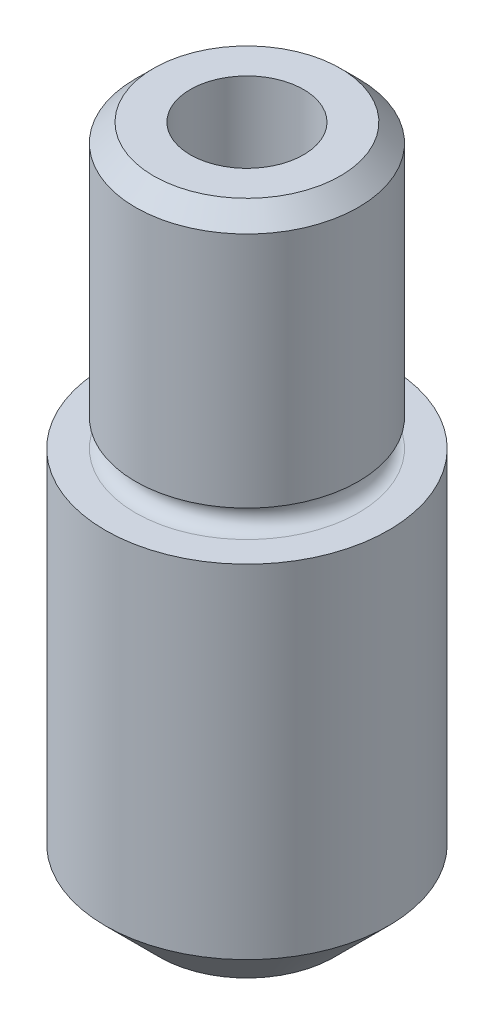
SolidWorks part; units mm, degrees
material "18-8 SS"
ref_plane "Front" through (0, 0, 0) normal (0, 0, 1) x (1, 0, 0)
ref_plane "Top" through (0, 0, 0) normal (0, 1, 0) x (1, 0, 0)
ref_plane "Right" through (0, 0, 0) normal (1, 0, 0) x (0, 0, -1)
sketch "Sketch1" plane through (0, 0, 0) normal (0, 1, 0) x (1, 0, 0)
  circle A0 centre (0, 0) radius 1.985
  dimension "D1" = 3.97
extrude "Base-Extrude" add sketch "Sketch1" along normal blind 9.525
sketch "Sketch2" plane through (0, 9.525, 0) normal (0, 1, 0) x (1, 0, 0)
  circle A0 centre (0, 0) radius 1.5621
  circle A1 centre (0, 0) radius 1.985
  circle A2 centre (0, 0) radius 1.985 construction
  dimension "D1" = 3.1242
extrude "Cut-Extrude2" cut sketch "Sketch2" against normal blind 3.9624
chamfer "Chamfer1" distance 0.254 angle 45 1 edges at (0, 9.525, 1.5621)
chamfer "Chamfer2" distance 0.762 angle 45 1 edges at (0, 0, 1.985)
sketch "Sketch4" plane through (0, 0, 0) normal (0, 0, 1) x (1, 0, 0)
  line L0 (1.985, 5.5626) -> (-1.985, 5.5626) construction
  line L1 (-1.5621, 9.271) -> (-1.5621, 5.5626) construction
  line L2 (0, 9.525) -> (0, 5.2816) construction
  line L3 (1.3081, 9.525) -> (-1.3081, 9.525) construction
  circle A0 centre (-1.5621, 5.7531) radius 0.1905
  dimension "D1" = 0.381
revolve "Cut-Revolve1" cut sketch "Sketch4" angle 360 about L2
hole_wizard "1/16 (0.0625) Diameter Hole1" positions "Sketch6" profile "Sketch5" hole size "1/16" standard "Ansi Inch" end condition through all
sketch "Sketch6" plane through (0, 9.525, 0) normal (0, 1, 0) x (-1, 0, 0)
  point P0 (0, 0)
sketch "Sketch5" plane through (0, 9.525, 0) normal (1, 0, 0) x (0, 0, 1)
  line L0 (0, 0) -> (0, 9.525)
  line L1 (0, 9.525) -> (0.7937, 9.525)
  line L2 (0.7937, 9.525) -> (0.7937, 0)
  line L5 (0.7937, 0) -> (0, 0)
  line L11 (0, -6.35) -> (0, 107.95) construction
  dimension "Thru Hole Dia." = 1.5875
  dimension "Thru Hole Depth" = 9.525
